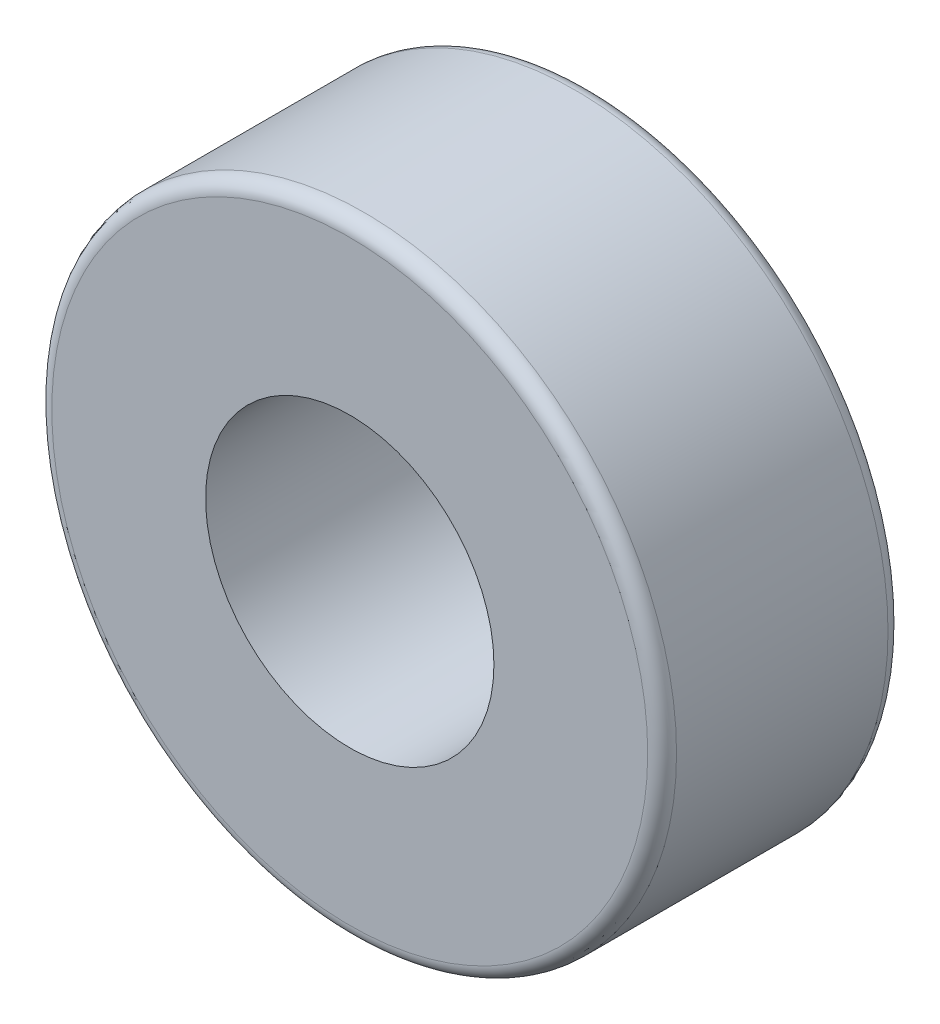
SolidWorks part; units mm, degrees
ref_plane "Front Plane" through (0, 0, 0) normal (0, 0, 1) x (1, 0, 0)
ref_plane "Top Plane" through (0, 0, 0) normal (0, 1, 0) x (1, 0, 0)
ref_plane "Right Plane" through (0, 0, 0) normal (1, 0, 0) x (0, 0, -1)
sketch "Sketch1" plane through (0, 0, 0) normal (0, 0, 1) x (1, 0, 0)
  circle A0 centre (0, 0) radius 6.5
  circle A1 centre (0, 0) radius 3
  dimension "D1" = 6
  dimension "D2" = 13
extrude "Boss-Extrude1" add sketch "Sketch1" along normal blind 5
fillet "Fillet1" radius 0.3 2 edges at (6.5, 0, 5) (6.5, 0, 0)
